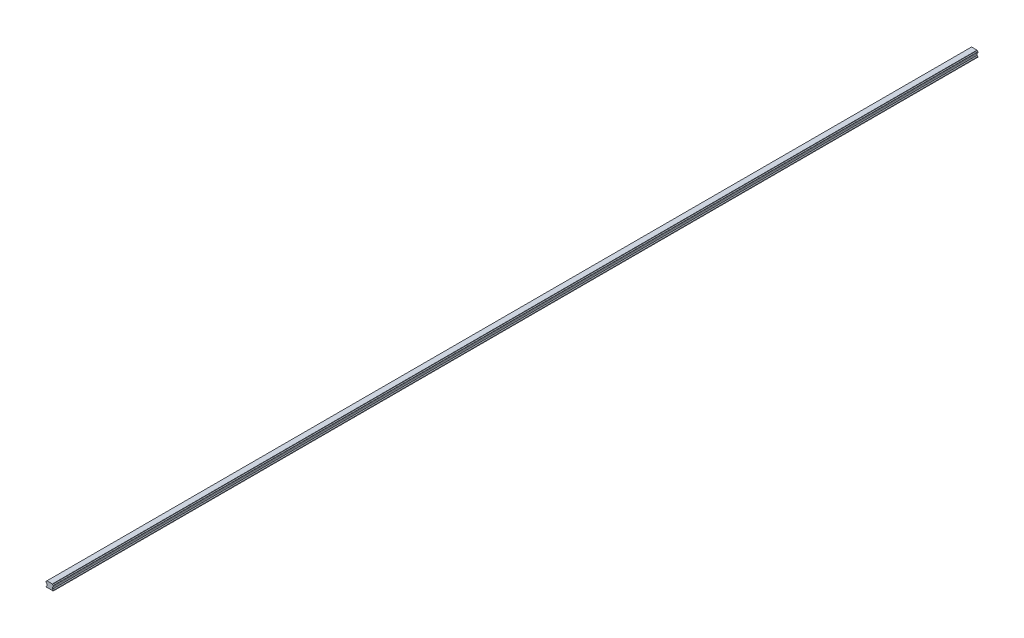
SolidWorks part; units mm, degrees
ref_plane "Piano frontale" through (0, 0, 0) normal (0, 0, 1) x (1, 0, 0)
ref_plane "Piano superiore" through (0, 0, 0) normal (0, 1, 0) x (1, 0, 0)
ref_plane "Piano destro" through (0, 0, 0) normal (1, 0, 0) x (0, 0, -1)
sketch "Schizzo1" plane through (0, 0, 0) normal (0, 0, 1) x (1, 0, 0)
  line L0 (-10.0871, -16.416) -> (-7.5656, -13.8945)
  line L1 (-7.5656, -13.8945) -> (-7.5656, -8.8516)
  line L2 (-7.5656, -8.8516) -> (-8.0776, -8.3396)
  line L3 (-10.3951, -6.0221) -> (-10.5914, -5.8258)
  line L4 (-10.5914, -5.8258) -> (-10.5914, -2.8001)
  line L5 (-10.5914, -2.8001) -> (-10.3951, -2.6038)
  line L6 (-8.0776, -0.2862) -> (-7.5656, 0.2257)
  line L7 (-7.5656, 0.2257) -> (9.5804, 0.2257)
  line L8 (9.5804, 0.2257) -> (10.0923, -0.2862)
  line L9 (12.4099, -2.6038) -> (12.6061, -2.8001)
  line L10 (12.6061, -2.8001) -> (12.6061, -5.8258)
  line L11 (12.6061, -5.8258) -> (12.4099, -6.0221)
  line L12 (10.0923, -8.3396) -> (9.5804, -8.8516)
  line L13 (9.5804, -8.8516) -> (9.5804, -13.8945)
  line L14 (9.5804, -13.8945) -> (12.1018, -16.416)
  line L16 (-10.0871, -16.416) -> (-10.0871, -17.7743)
  line L17 (-10.0871, -17.7743) -> (12.1018, -17.7743)
  line L18 (12.1018, -17.7743) -> (12.1018, -16.416)
  arc A0 (-8.0776, -8.3396) -> (-10.3951, -6.0221) centre (-10.5914, -8.5359) ccw
  arc A1 (-10.3951, -2.6038) -> (-8.0776, -0.2862) centre (-10.5914, -0.09) ccw
  arc A2 (10.0923, -0.2862) -> (12.4099, -2.6038) centre (12.6061, -0.09) ccw
  arc A3 (12.4099, -6.0221) -> (10.0923, -8.3396) centre (12.6061, -8.5359) ccw
  dimension "D1" = 18
extrude "Estrusione-Estrusione1" add sketch "Schizzo1" along direction (0, 0, 1) on the side of the normal blind 2897 from surface at 0 starting at plane "Piano frontale"
